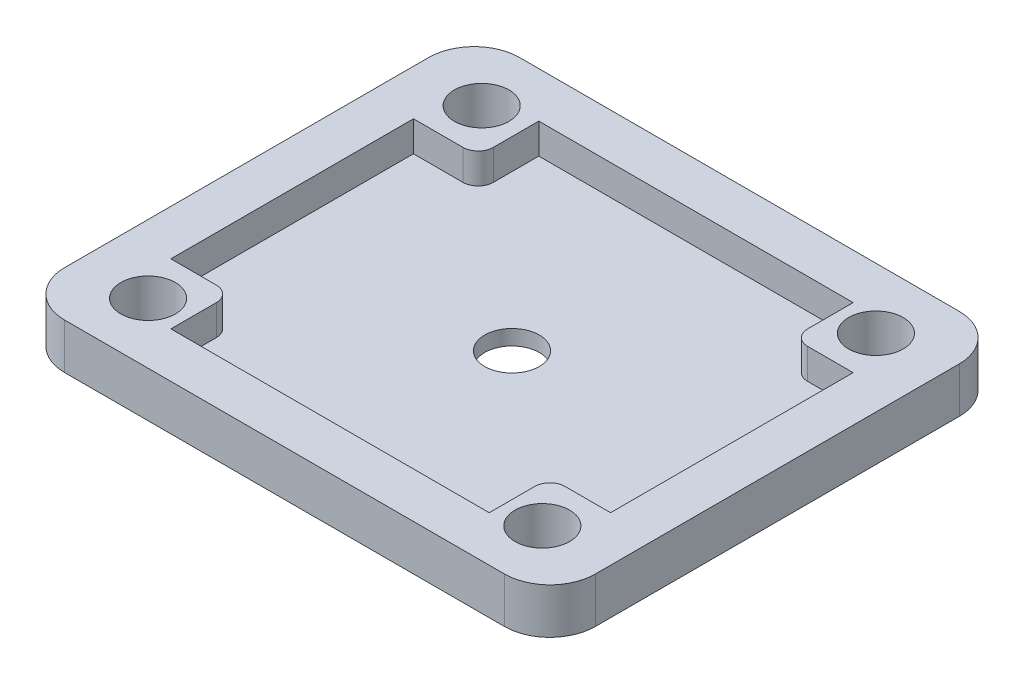
SolidWorks part; units mm, degrees
ref_plane "Front Plane" through (0, 0, 0) normal (0, 0, 1) x (1, 0, 0)
ref_plane "Top Plane" through (0, 0, 0) normal (0, 1, 0) x (1, 0, 0)
ref_plane "Right Plane" through (0, 0, 0) normal (1, 0, 0) x (0, 0, -1)
sketch "Sketch1" plane through (0, 0, 0) normal (0, 1, 0) x (1, 0, 0)
  line L1 (-17.5, -15) -> (17.5, -15)
  line L2 (-17.5, -15) -> (-17.5, 15)
  line L3 (-17.5, 15) -> (17.5, 15)
  line L4 (17.5, -15) -> (17.5, 15)
  line L5 (-17.5, -15) -> (17.5, 15) construction
  line L6 (-17.5, 15) -> (17.5, -15) construction
  point P0 (0, 0)
  dimension "D1" = 30
  dimension "D2" = 35
extrude "Boss-Extrude1" add sketch "Sketch1" along normal blind 3
sketch "Sketch2" plane through (0, 3, 0) normal (0, 1, 0) x (1, 0, 0)
  line L8 (14.5, -12) -> (14.5, 12)
  line L9 (14.5, 12) -> (-14.5, 12)
  line L10 (-14.5, 12) -> (-14.5, -12)
  line L11 (-14.5, -12) -> (14.5, -12)
  line L12 (14.5, -12) -> (14.5, 12)
  line L13 (14.5, 12) -> (-14.5, 12)
  line L14 (-14.5, 12) -> (-14.5, -12)
  line L15 (-14.5, -12) -> (14.5, -12)
  dimension "D1" = 3
extrude "Cut-Extrude1" cut sketch "Sketch2" against normal blind 2
sketch "Sketch5" plane through (0, 1, 0) normal (0, 1, 0) x (1, 0, 0)
  line L1 (-14.5, 12) -> (-10.2337, 12)
  line L2 (-14.5, 12) -> (-14.5, 8)
  line L3 (-14.5, 8) -> (-10.2337, 8)
  line L4 (-10.2337, 12) -> (-10.2337, 8)
  line L5 (14.5, 12) -> (10.5, 12)
  line L6 (14.5, 12) -> (14.5, 8)
  line L7 (14.5, 8) -> (10.5, 8)
  line L8 (10.5, 12) -> (10.5, 8)
  line L9 (14.5, -12) -> (10.5, -12)
  line L10 (14.5, -12) -> (14.5, -8)
  line L11 (14.5, -8) -> (10.5, -8)
  line L12 (10.5, -12) -> (10.5, -8)
  line L13 (-14.5, -12) -> (-10.5, -12)
  line L14 (-14.5, -12) -> (-14.5, -8)
  line L15 (-14.5, -8) -> (-10.5, -8)
  line L16 (-10.5, -12) -> (-10.5, -8)
  dimension "D1" = 4
  dimension "D2" = 4
extrude "Boss-Extrude2" add sketch "Sketch5" along normal blind 2
hole_wizard "M3 Clearance Hole1" positions "Sketch3" profile "Sketch4" hole size "M3" standard "ANSI Metric" end condition through all
sketch "Sketch3" plane through (0, 3, 0) normal (0, 1, 0) x (1, 0, 0)
  line L1 (-13, -11) -> (13, -11)
  line L2 (-13, -11) -> (-13, 11)
  line L3 (-13, 11) -> (13, 11)
  line L4 (13, -11) -> (13, 11)
  line L5 (-13, -11) -> (13, 11) construction
  line L6 (-13, 11) -> (13, -11) construction
  point P1 (0, 0)
  point P2 (13, 11)
  point P73 (-13, -11)
  point P74 (-13, 11)
  point P75 (13, -11)
  dimension "D1" = 26
  dimension "D2" = 22
sketch "Sketch4" plane through (0, 3, 0) normal (1, 0, 0) x (0, 0, 1)
  line L0 (0, 0) -> (0, 3)
  line L1 (0, 3) -> (1.8, 3)
  line L2 (1.8, 3) -> (1.8, 0)
  line L5 (1.8, 0) -> (0, 0)
  line L11 (0, -6.35) -> (0, 107.95) construction
  dimension "Thru Hole Dia." = 3.6
  dimension "Thru Hole Depth" = 3
fillet "Fillet1" radius 3 4 edges at (17.5, 1.5, 15) (-17.5, 1.5, 15) (-17.5, 1.5, -15) (17.5, 1.5, -15)
fillet "Fillet2" radius 1 4 edges at (-10.5, 2, 8) (10.5, 2, 8) (10.5, 2, -8) (-10.2337, 2, -8)
